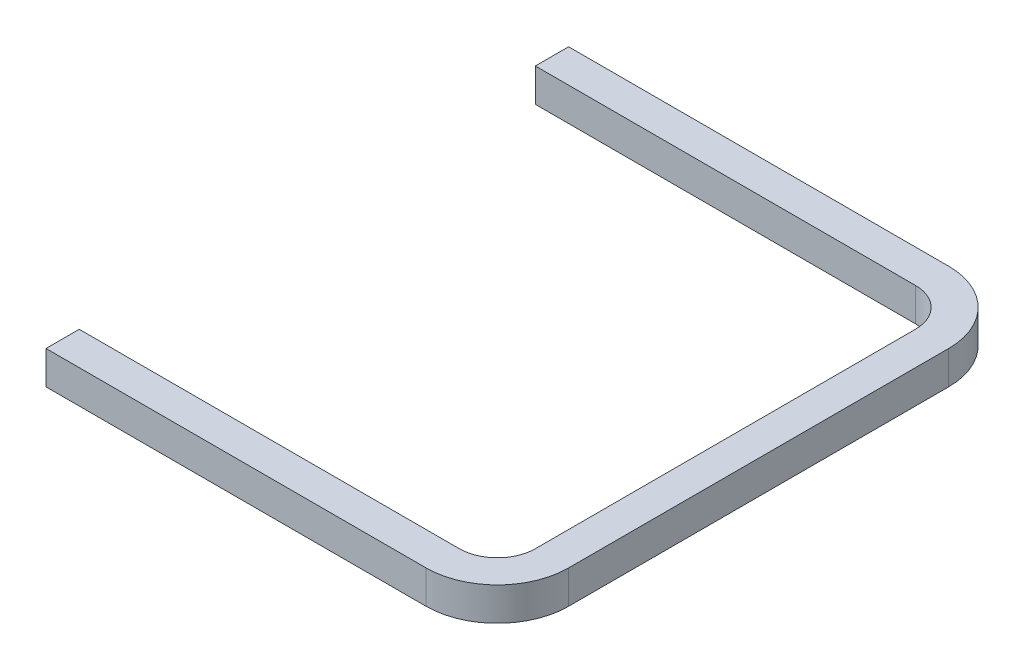
SolidWorks part; units mm, degrees
ref_plane "Front Plane" through (0, 0, 0) normal (0, 0, 1) x (1, 0, 0)
ref_plane "Top Plane" through (0, 0, 0) normal (0, 1, 0) x (1, 0, 0)
ref_plane "Right Plane" through (0, 0, 0) normal (1, 0, 0) x (0, 0, -1)
sketch "Sketch2" plane through (0, 0, 0) normal (0, 1, 0) x (1, 0, 0)
  line L0 (0, 152.4) -> (0, 0) construction
  line L5 (127, -152.4) -> (-127, -152.4)
  line L6 (152.4, -127) -> (152.4, 127)
  line L7 (127, 152.4) -> (-127, 152.4)
  line L9 (0, 0) -> (0, -152.4) construction
  line L10 (0, 0) -> (152.4, 0) construction
  arc A0 (127, -152.4) -> (152.4, -127) centre (127, -127) ccw
  arc A1 (152.4, 127) -> (127, 152.4) centre (127, 127) ccw
  dimension "D2" = 25.4
  dimension "D1" = 279.4
extrude "Extrude-Thin1" add sketch "Sketch2" along normal blind 22.225 thin thin type one direction reverse wall 22.225
